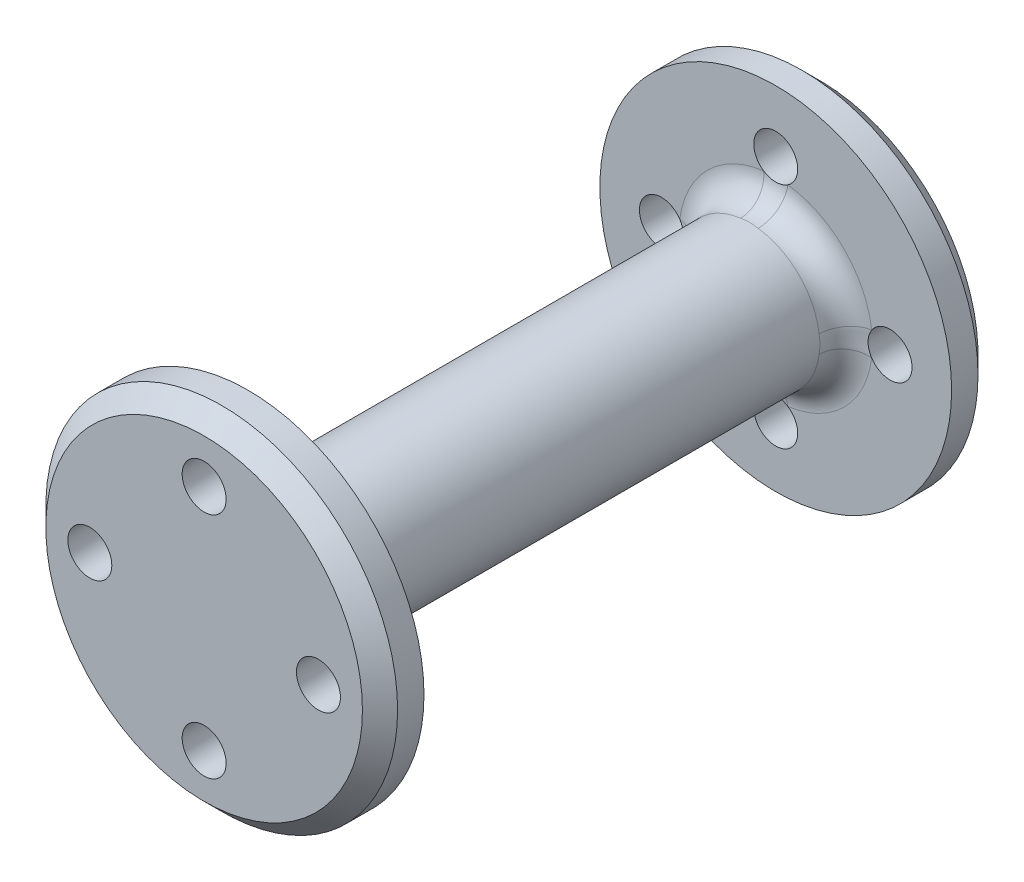
SolidWorks part; units mm, degrees
ref_plane "Front Plane" through (0, 0, 0) normal (0, 0, 1) x (1, 0, 0)
ref_plane "Top Plane" through (0, 0, 0) normal (0, 1, 0) x (1, 0, 0)
ref_plane "Right Plane" through (0, 0, 0) normal (1, 0, 0) x (0, 0, -1)
sketch "Sketch1" plane through (0, 0, 0) normal (0, 0, 1) x (1, 0, 0)
  circle A0 centre (0, 0) radius 8
  dimension "ShaftDiameter" = 16
extrude "Boss-Extrude1" add sketch "Sketch1" along normal mid plane 60
sketch "Sketch2" plane through (0, 0, 30) normal (0, 0, 1) x (1, 0, 0)
  circle A0 centre (0, 0) radius 20
  dimension "CapDiameter" = 40
extrude "Boss-Extrude2" add sketch "Sketch2" along normal blind 5
chamfer "Chamfer1" distance 2 angle 45 1 edges at (20, 0, 35)
sketch "Sketch3" plane through (0, 0, 35) normal (0, 0, 1) x (1, 0, 0)
  line L0 (0, 8) -> (0, 18) construction
  circle A0 centre (0, 0) radius 8 construction
  circle A1 centre (0, 0) radius 18 construction
  circle A2 centre (0, 13) radius 2.5
  dimension "D1" = 5
extrude "Cut-Extrude1" cut sketch "Sketch3" against normal through all
pattern_circular "CirPattern1" count 4 over 360 about axis through (0, 0, 0) along (0, 0, 1) of "Cut-Extrude1"
fillet "Fillet1" radius 3 1 edges at (8, 0, 30)
hole_wizard "CBORE for #12 Binding Head Machine Screw1" positions "Sketch5" profile "Sketch6" counterbore size "#12" standard "ANSI Inch"
sketch "Sketch5" plane through (0, 0, 35) normal (0, 0, 1) x (1, 0, 0)
  point P0 (0, 0)
sketch "Sketch6" plane through (0, 0, 35) normal (1, 0, 0) x (0, -1, 0)
  line L0 (0, 0) -> (0, 70)
  line L1 (0, 70) -> (3.1242, 70)
  line L3 (3.1242, 70) -> (3.1242, 3.5814)
  line L4 (5.9538, 3.5814) -> (3.1242, 3.5814)
  line L5 (5.9538, 3.5814) -> (5.9538, 0.635)
  line L6 (5.9538, 0.635) -> (6.5888, 0)
  line L7 (6.5888, 0) -> (0, 0)
  line L8 (-5.9538, 0.635) -> (-6.5888, 0) construction
  line L11 (0, -6.35) -> (0, 107.95) construction
  dimension "Thru Hole Dia." = 6.2484
  dimension "Thru Hole Depth" = 70
  dimension "C'Bore Dia." = 11.9075
  dimension "C'Bore Depth" = 3.5814
  dimension "Near C'Sink Dia." = 13.1775
  dimension "Near C'Sink Angle" = 90
mirror "Mirror5" about plane through (0, 0, 0) normal (0, 0, 1) of "CBORE for #12 Binding Head Machine Screw1", "Boss-Extrude2", "Chamfer1", "Cut-Extrude1", "CirPattern1", "Fillet1"
